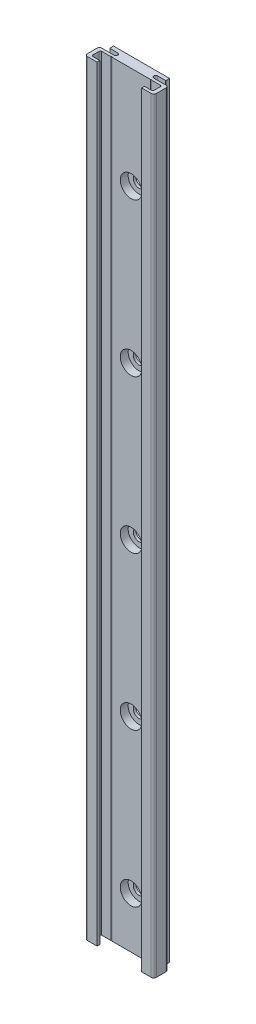
SolidWorks part; units mm, degrees
ref_plane "Front Plane" through (0, 0, 0) normal (0, 0, 1) x (1, 0, 0)
ref_plane "Top Plane" through (0, 0, 0) normal (0, 1, 0) x (1, 0, 0)
ref_plane "Right Plane" through (0, 0, 0) normal (1, 0, 0) x (0, 0, -1)
ref_plane "Plane1" through (0, 300, 0) normal (0, 1, 0) x (1, 0, 0)
sketch "Sketch1" plane through (0, 300, 0) normal (0, 1, 0) x (1, 0, 0)
  line L0 (-13.5, -3) -> (-13.5, -8.7)
  line L1 (-13.5, -8.7) -> (13.5, -8.7)
  line L2 (13.5, -8.7) -> (13.5, -3)
  line L3 (13.5, -3) -> (7.8, -3)
  line L4 (7.8, -1.5) -> (11, -1.5)
  line L5 (11, -1.5) -> (11, 0)
  line L6 (11, 0) -> (-11, 0)
  line L7 (-11, 0) -> (-11, -1.5)
  line L8 (-11, -1.5) -> (-7.8, -1.5)
  line L9 (-7.8, -3) -> (-13.5, -3)
  arc A0 (7.8, -3) -> (7.8, -1.5) centre (7.8, -2.25) cw
  arc A1 (-7.8, -1.5) -> (-7.8, -3) centre (-7.8, -2.25) cw
extrude "Boss-Extrude1" add sketch "Sketch1" against normal blind 300
sketch "Sketch2" plane through (0, 0, 0) normal (0, -1, 0) x (1, 0, 0)
  line L0 (8.75, 8.7) -> (-8.75, 8.7)
  line L1 (-8.75, 8.7) -> (-8.75, 7.6)
  line L2 (-8.75, 7.6) -> (-12, 7.6)
  line L3 (-12, 7.6) -> (-12, 4.1)
  line L4 (-12, 4.1) -> (12, 4.1)
  line L5 (12, 4.1) -> (12, 7.6)
  line L6 (12, 7.6) -> (8.75, 7.6)
  line L7 (8.75, 7.6) -> (8.75, 8.7)
extrude "Cut-Extrude1" cut sketch "Sketch2" against normal through all
hole_wizard "Ø0.4 (0.4) Diameter Hole1" positions "Sketch4" profile "Sketch3" hole size "Ø0.4" standard "ANSI Metric"
sketch "Sketch4" plane through (0, 300, 0) normal (0, 1, 0) x (1, 0, 0)
  point P0 (-7.75, -4.1)
  point P1 (7.75, -4.1)
sketch "Sketch3" plane through (-7.75, 300, 4.1) normal (1, 0, 0) x (0, 0, 1)
  line L0 (0, 0) -> (0, 300)
  line L1 (0, 300) -> (0.2, 300)
  line L2 (0.2, 300) -> (0.2, 0)
  line L5 (0.2, 0) -> (0, 0)
  line L11 (0, -6.35) -> (0, 107.95) construction
  dimension "Thru Hole Dia." = 0.4
  dimension "Thru Hole Depth" = 300
hole_wizard "CBORE for M4 Hex Head Machine Screw1" positions "Sketch6" profile "Sketch5" counterbore size "M4" standard "ANSI Metric"
sketch "Sketch6" plane through (0, 0, 4.1) normal (0, 0, 1) x (1, 0, 0)
  point P0 (0, 260)
  point P1 (0, 200)
  point P2 (0, 140)
  point P3 (0, 80)
  point P4 (0, 20)
sketch "Sketch5" plane through (0, 260, 4.1) normal (1, 0, 0) x (0, -1, 0)
  line L0 (0, 0) -> (0, 4.1)
  line L1 (0, 4.1) -> (2.25, 4.1)
  line L3 (2.25, 4.1) -> (2.25, 3.1)
  line L4 (2.25, 3.1) -> (4.25, 3.1)
  line L5 (4.25, 3.1) -> (4.25, 0)
  line L7 (4.25, 0) -> (0, 0)
  line L11 (0, -6.35) -> (0, 107.95) construction
  dimension "Thru Hole Dia." = 4.5
  dimension "Thru Hole Depth" = 4.1
  dimension "C'Bore Dia." = 8.5
  dimension "C'Bore Depth" = 3.1
fillet "Fillet1" radius 0.2 2 edges at (11, 150, 1.5) (-11, 150, 1.5)
fillet "Fillet2" radius 0.5 4 edges at (12, 150, 4.1) (-12, 150, 7.6) (12, 150, 7.6) (-12, 150, 4.1)
fillet "Fillet3" radius 1 4 edges at (-13.5, 150, 8.7) (-13.5, 150, 3) (13.5, 150, 3) (13.5, 150, 8.7)
